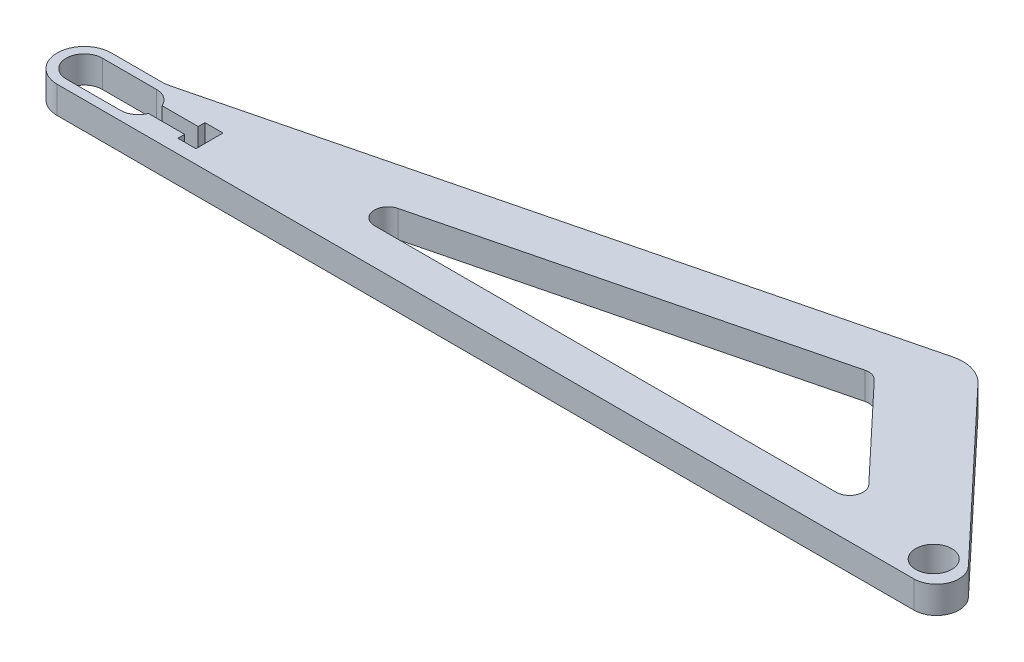
SolidWorks part; units mm, degrees
material "Pine"
ref_plane "Front Plane" through (0, 0, 0) normal (0, 0, 1) x (1, 0, 0)
ref_plane "Top Plane" through (0, 0, 0) normal (0, 1, 0) x (1, 0, 0)
ref_plane "Right Plane" through (0, 0, 0) normal (1, 0, 0) x (0, 0, -1)
sketch "Sketch1" plane through (0, 0, 0) normal (0, 1, 0) x (1, 0, 0)
  line L0 (0, -31.4854) -> (0, 62.351) construction
  line L1 (0, -19.05) -> (-558.8, -19.05)
  line L2 (-555.7665, 19.8084) -> (-116.049, 129.7377)
  line L3 (-91.3924, 122.5044) -> (0, 25.4)
  line L4 (-561.9269, 19.05) -> (-596.9, 19.05)
  line L5 (-558.8, -19.05) -> (-596.9, -19.05)
  line L6 (-596.9, -12.7) -> (-558.8, -12.7)
  line L7 (-596.9, 12.7) -> (-558.8, 12.7)
  line L8 (-546.1, 0) -> (-495.6463, 0) construction
  line L9 (-547.0268, -4.7625) -> (-521.6268, -4.7625)
  line L10 (-521.6268, -4.7625) -> (-521.6268, -9.525)
  line L11 (-521.6268, -9.525) -> (-508.9268, -9.525)
  line L12 (-508.9268, -9.525) -> (-508.9268, 9.525)
  line L13 (-521.6268, 9.525) -> (-508.9268, 9.525)
  line L14 (-521.6268, 4.7625) -> (-521.6268, 9.525)
  line L15 (-547.0268, 4.7625) -> (-521.6268, 4.7625)
  line L16 (0, -19.05) -> (5.0938, -19.05)
  line L17 (0, 25.4) -> (16.654, 7.7052)
  line L18 (-401.6665, 25.1156) -> (-139.0811, 90.762)
  line L19 (-129.8348, 88.0495) -> (-68.05, 22.4031)
  line L20 (-74.9861, 6.35) -> (-399.3564, 6.35)
  circle A0 centre (0, 0) radius 12.7
  arc A1 (-558.8, -12.7) -> (-547.0268, -4.7625) centre (-558.8, 0) ccw
  arc A2 (-596.9, 12.7) -> (-596.9, -12.7) centre (-596.9, 0) ccw
  arc A3 (-596.9, 19.05) -> (-596.9, -19.05) centre (-596.9, 0) ccw
  arc A4 (-547.0268, 4.7625) -> (-558.8, 12.7) centre (-558.8, 0) ccw
  arc A5 (-555.7665, 19.8084) -> (-561.9269, 19.05) centre (-561.9269, 44.45) cw
  arc A6 (-116.049, 129.7377) -> (-91.3924, 122.5044) centre (-109.8886, 105.0961) cw
  arc A7 (16.654, 7.7052) -> (5.0938, -19.05) centre (5.0938, -3.175) cw
  arc A8 (-401.6665, 25.1156) -> (-399.3564, 6.35) centre (-399.3564, 15.875) ccw
  arc A9 (-139.0811, 90.762) -> (-129.8348, 88.0495) centre (-136.7709, 81.5214) cw
  arc A10 (-68.05, 22.4031) -> (-74.9861, 6.35) centre (-74.9861, 15.875) cw
  point P26 (-508.9268, 0)
  point P31 (-558.8, 19.05)
  point P34 (-101.6, 133.35)
  dimension "D1" = 25.4
  dimension "D5" = 25.4
  dimension "D8" = 25.4
  dimension "D14" = 25.4
  dimension "D15" = 25.4
  dimension "D18" = 15.875
  dimension "D19" = 9.525
  dimension "D2" = 558.8
  dimension "D3" = 152.4
  dimension "D4" = 101.6
  dimension "D6" = 19.05
  dimension "D7" = 19.05
  dimension "D9" = 38.1
  dimension "D10" = 9.525
  dimension "D11" = 4.7625
  dimension "D12" = 12.7
  dimension "D13" = 25.4
  dimension "D16" = 19.05
  dimension "D17" = 25.4
  dimension "D20" = 0
  dimension "D21" = 25.4
  dimension "D22" = 0
extrude "Boss-Extrude1" add sketch "Sketch1" along normal blind 19.05
